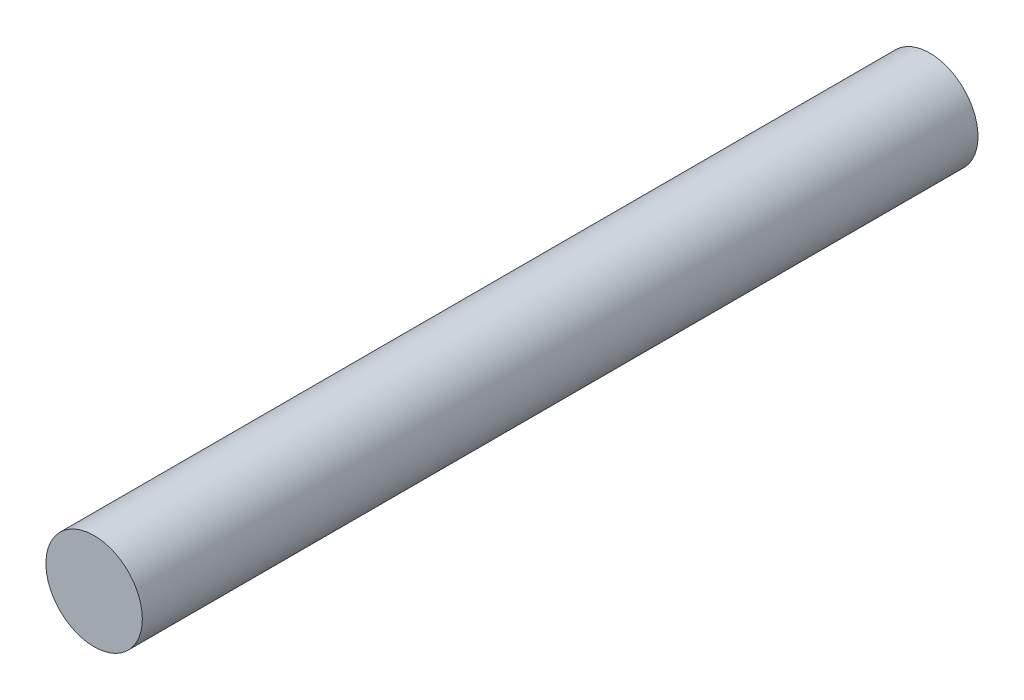
SolidWorks part; units mm, degrees
ref_plane "Front Plane" through (0, 0, 0) normal (0, 0, 1) x (1, 0, 0)
ref_plane "Top Plane" through (0, 0, 0) normal (0, 1, 0) x (1, 0, 0)
ref_plane "Right Plane" through (0, 0, 0) normal (1, 0, 0) x (0, 0, -1)
sketch "Sketch1" plane through (0, 0, 0) normal (0, 0, 1) x (1, 0, 0)
  circle A0 centre (0, 0) radius 3
  dimension "D1" = 6
extrude "Boss-Extrude1" add sketch "Sketch1" along normal blind 52
